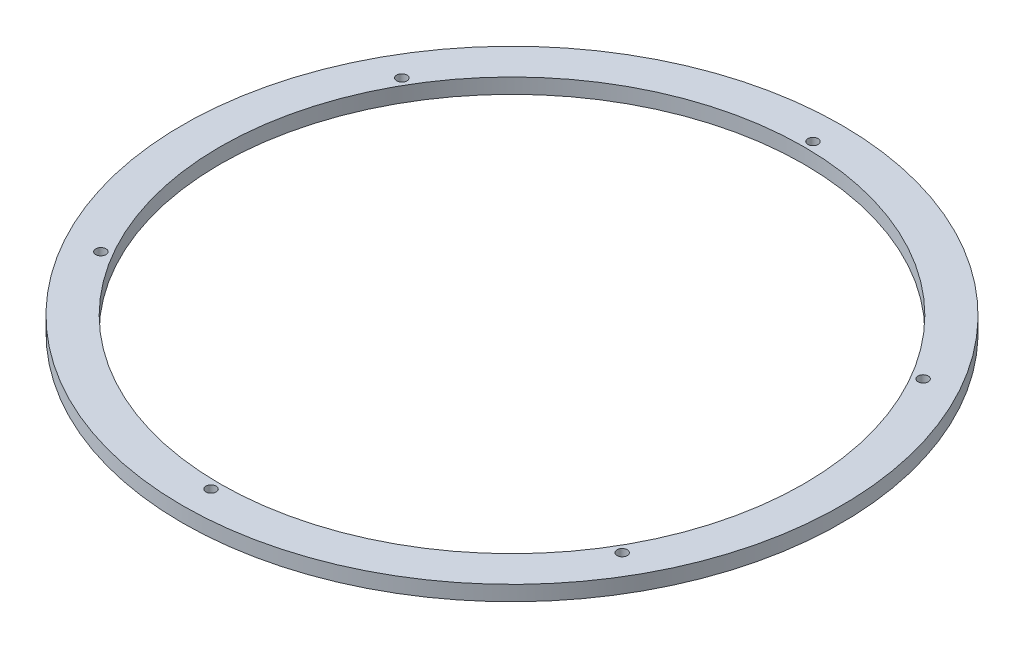
SolidWorks part; units mm, degrees
ref_plane "Front Plane" through (0, 0, 0) normal (0, 0, 1) x (1, 0, 0)
ref_plane "Top Plane" through (0, 0, 0) normal (0, 1, 0) x (1, 0, 0)
ref_plane "Right Plane" through (0, 0, 0) normal (1, 0, 0) x (0, 0, -1)
sketch "Sketch1" plane through (0, 0, 0) normal (0, 1, 0) x (1, 0, 0)
  circle A0 centre (0, 0) radius 98.552
  circle A1 centre (0, 0) radius 111.252
  dimension "D1" = 197.104
  dimension "D2" = 12.7
extrude "Boss-Extrude1" add sketch "Sketch1" along normal blind 5.08
hole_wizard "Tap Drill for #8-32 Tap1" positions "Sketch2" profile "Sketch3" hole size "#8-32" standard "ANSI Inch"
sketch "Sketch2" plane through (0, 5.08, 0) normal (0, 1, 0) x (1, 0, 0)
  point P0 (-87.9882, 50.8)
  point P3 (0, 101.6)
  point P6 (87.9882, 50.8)
  point P9 (87.9882, -50.8)
  point P12 (0, -101.6)
  point P15 (-87.9882, -50.8)
sketch "Sketch3" plane through (-87.9882, 5.08, -50.8) normal (1, 0, 0) x (0, 0, 1)
  line L0 (0, 0) -> (0, 26.4378)
  line L1 (0, 26.4378) -> (1.7272, 25.4)
  line L2 (1.7272, 25.4) -> (1.7272, 0)
  line L5 (1.7272, 0) -> (0, 0)
  line L10 (0, 26.4378) -> (-1.7272, 25.4) construction
  line L11 (0, -6.35) -> (0, 107.95) construction
  dimension "Hole Dia." = 3.4544
  dimension "Hole Depth" = 25.4
  dimension "Drill Angle" = 118
